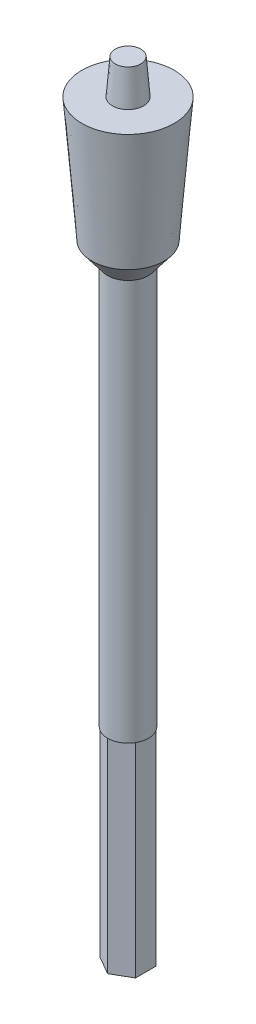
SolidWorks part; units mm, degrees
material "Plain Carbon Steel"
ref_plane "Front Plane" through (0, 0, 0) normal (0, 0, 1) x (1, 0, 0)
ref_plane "Top Plane" through (0, 0, 0) normal (0, 1, 0) x (1, 0, 0)
ref_plane "Right Plane" through (0, 0, 0) normal (1, 0, 0) x (0, 0, -1)
sketch "Sketch1" plane through (0, 0, 0) normal (0, 0, 1) x (1, 0, 0)
  line L0 (0, 0) -> (0, 153)
  line L2 (2.6861, 128.6377) -> (7.9187, 128.6377)
  line L3 (7.9187, 128.6377) -> (6.2137, 107.3201)
  line L4 (6.2137, 107.3201) -> (3.5, 103.7948)
  line L5 (3.5, 103.7948) -> (3.5, 55)
  line L6 (3.5, 0) -> (0, 0)
  line L7 (2.6861, 128.6377) -> (0.7264, 153)
  line L8 (0, 153) -> (0.7264, 153)
  line L12 (3.5, 53) -> (3.5, 0)
  line L13 (3.5, 55) -> (3.5, 53)
  dimension "D1" = 3.5
  dimension "D2" = 153
revolve "Revolve1" add sketch "Sketch1" angle 360 about L0
sketch "Sketch2" plane through (0, 0, 0) normal (0, -1, 0) x (1, 0, 0)
  line L1 (0, 3.5) -> (-3.0311, 1.75)
  line L2 (-3.0311, 1.75) -> (-3.0311, -1.75)
  line L3 (-3.0311, -1.75) -> (0, -3.5)
  line L4 (0, -3.5) -> (3.0311, -1.75)
  line L5 (3.0311, -1.75) -> (3.0311, 1.75)
  line L6 (3.0311, 1.75) -> (0, 3.5)
  circle A0 centre (0, 0) radius 3.0311 construction
  circle A1 centre (0, 0) radius 4.3881
  dimension "D1" = 6.0622
extrude "Cut-Extrude1" cut sketch "Sketch2" against normal blind 35
ref_plane "Plane1" through (0, 134.6377, 0) normal (0, 1, 0) x (1, 0, 0)
sketch "Sketch4" plane through (0, 134.6377, 0) normal (0, 1, 0) x (1, 0, 0)
  circle A0 centre (0, 0) radius 12.1375
extrude "Cut-Extrude2" cut sketch "Sketch4" along normal through all
